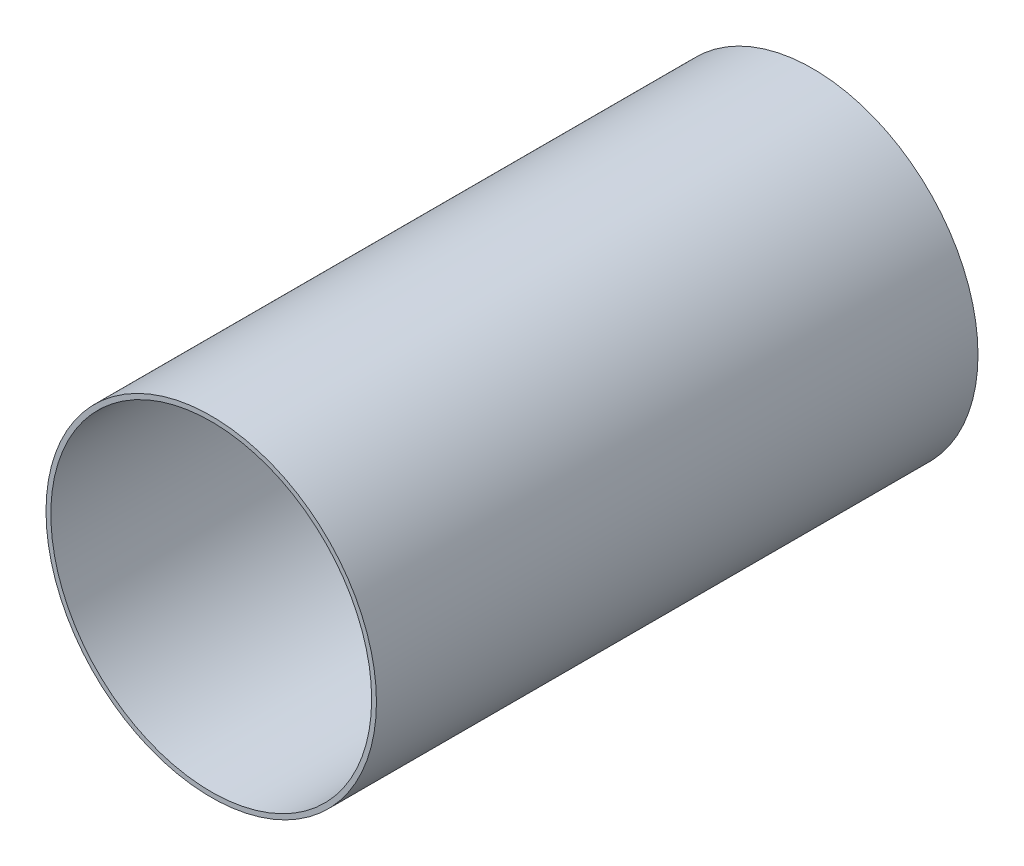
SolidWorks part; units mm, degrees
ref_plane "Plan de face" through (0, 0, 0) normal (0, 0, 1) x (1, 0, 0)
ref_plane "Plan de dessus" through (0, 0, 0) normal (0, 1, 0) x (1, 0, 0)
ref_plane "Plan de droite" through (0, 0, 0) normal (1, 0, 0) x (0, 0, -1)
sketch "Esquisse1" plane through (0, 0, 0) normal (0, 0, 1) x (1, 0, 0)
  circle A0 centre (0, 0) radius 40
  circle A1 centre (0, 0) radius 41.2
  dimension "D1" = 80
  dimension "D2" = 1.2
extrude "Boss.-Extru.1" add sketch "Esquisse1" along normal blind 150
